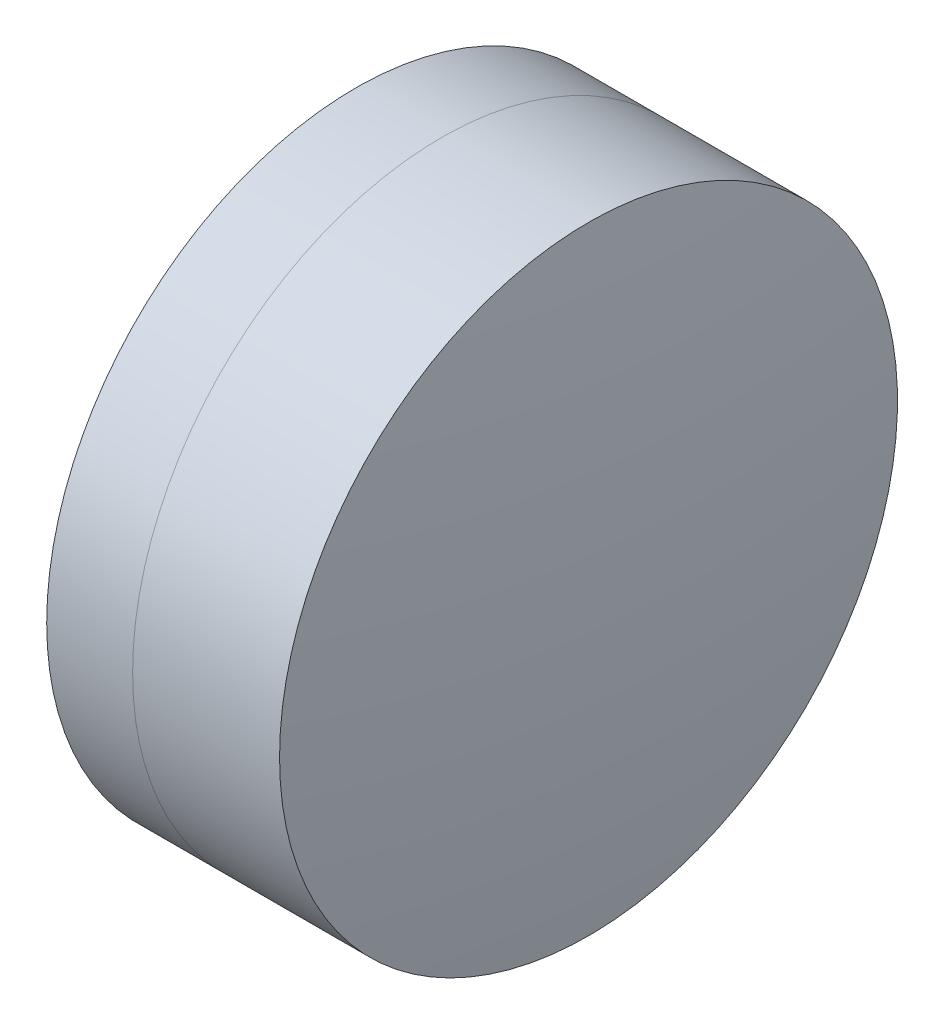
SolidWorks part; units mm, degrees
ref_plane "前视基准面" through (0, 0, 0) normal (0, 0, 1) x (1, 0, 0)
ref_plane "上视基准面" through (0, 0, 0) normal (0, 1, 0) x (1, 0, 0)
ref_plane "右视基准面" through (0, 0, 0) normal (1, 0, 0) x (0, 0, -1)
sketch "草图1" plane through (0, 0, 0) normal (0, 1, 0) x (1, 0, 0)
  line L0 (-9.7026, 0) -> (238.8542, 0) construction
  line L1 (218.8777, -12.7) -> (222.4082, -12.7)
  line L2 (218.8777, 12.7) -> (222.4082, 12.7)
  arc A0 (222.4082, -12.7) -> (222.4082, 12.7) centre (208.1422, 0) ccw
  arc A1 (218.8777, 12.7) -> (218.8777, -12.7) centre (239.2422, 0) ccw
  point P10 (215.2422, 0)
  point P11 (227.2422, 0)
  dimension "D3" = 24
  dimension "D4" = 19.1
  dimension "D1" = 12.7
  dimension "D2" = 12.7
  dimension "D5" = 12
revolve "旋转1" add sketch "草图1" angle 360 about L0
sketch "草图2" plane through (0, 0, 0) normal (0, 1, 0) x (1, 0, 0)
  line L0 (-0.5519, 0) -> (253.9868, 0) construction
  line L2 (222.4082, 12.7) -> (228.4492, 12.7)
  line L3 (222.4082, -12.7) -> (228.4492, -12.7)
  arc A0 (228.4492, -12.7) -> (228.4492, 12.7) centre (127.1422, 0) ccw
  arc A1 (222.4082, -12.7) -> (222.4082, 12.7) centre (208.1422, 0) ccw construction
  arc A2 (222.4082, -12.7) -> (222.4082, 12.7) centre (208.1422, 0) ccw
  point P4 (227.2422, 0)
  point P8 (229.2422, 0)
  dimension "D1" = 102.1
  dimension "D2" = 2
revolve "旋转3" add sketch "草图2" angle 360 about L0
